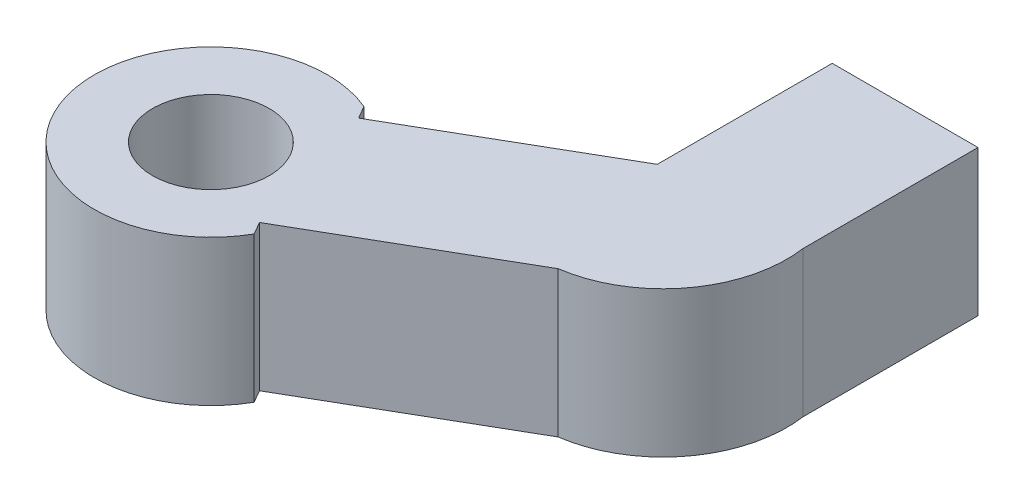
SolidWorks part; units mm, degrees
ref_plane "Front Plane" through (0, 0, 0) normal (0, 0, 1) x (1, 0, 0)
ref_plane "Top Plane" through (0, 0, 0) normal (0, 1, 0) x (1, 0, 0)
ref_plane "Right Plane" through (0, 0, 0) normal (1, 0, 0) x (0, 0, -1)
sketch "Sketch1" plane through (0, 0, 0) normal (0, 1, 0) x (1, 0, 0)
  line L0 (0, 0) -> (-6.4952, -3.75)
  line L2 (0, 0) -> (0, 6)
  line L3 (0, 6) -> (5, 6)
  line L4 (5, 0) -> (5, 6)
  line L7 (1.4, -4.8) -> (-5.0952, -8.55)
  line L8 (-6.4952, -3.75) -> (-6.7452, -3.317)
  line L9 (-5.0952, -8.55) -> (-4.8452, -8.983)
  arc A0 (1.4, -4.8) -> (5, 0) centre (0.7917, -0.5938) ccw
  arc A1 (-6.7452, -3.317) -> (-4.8452, -8.983) centre (-8.3164, -6.9955) ccw
  circle A2 centre (-8.3164, -6.9955) radius 2
  dimension "D5" = 4.25
  dimension "D6" = 5
  dimension "D7" = 6
  dimension "D8" = 4
  dimension "D10" = 4
  dimension "D1" = 6
  dimension "D2" = 7.5
  dimension "D3" = 5
  dimension "D4" = 0.5
  dimension "D9" = 120
extrude "Boss-Extrude2" add sketch "Sketch1" along normal mid plane 5
